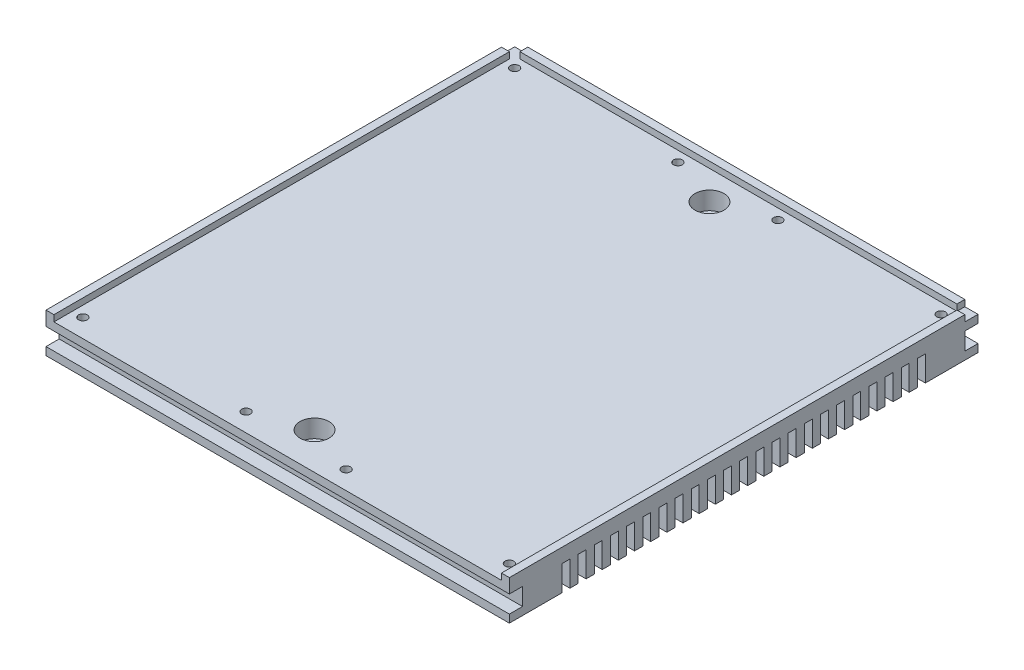
SolidWorks part; units mm, degrees
material "6061 合金"
ref_plane "前视基准面" through (0, 0, 0) normal (0, 0, 1) x (1, 0, 0)
ref_plane "上视基准面" through (0, 0, 0) normal (0, 1, 0) x (1, 0, 0)
ref_plane "右视基准面" through (0, 0, 0) normal (1, 0, 0) x (0, 0, -1)
sketch "草图1" plane through (0, 12.6, 0) normal (0, 1, 0) x (1, 0, 0)
  line L0 (-100.7481, -361.7245) -> (-100.7481, -517.7245) construction
  line L1 (72.2519, -528.7245) -> (-103.7481, -528.7245)
  line L2 (72.2519, -528.7245) -> (72.2519, -350.7245)
  line L3 (72.2519, -350.7245) -> (-103.7481, -350.7245)
  line L4 (-103.7481, -528.7245) -> (-103.7481, -350.7245)
  line L5 (7.2519, -525.7245) -> (61.2519, -525.7245) construction
  line L6 (69.2519, -517.7245) -> (69.2519, -361.7245) construction
  line L9 (61.2519, -353.7245) -> (7.2519, -353.7245) construction
  dimension "D1" = 3
  dimension "D2" = 3
  dimension "D3" = 3
  dimension "D4" = 3
extrude "凸台-拉伸1" add sketch "草图1" against normal up to surface (12.6 mm away)
sketch "草图3" plane through (0, 12.6, 0) normal (0, 1, 0) x (1, 0, 0)
  line L0 (-15.7481, -539.7245) -> (-15.7481, -489.7245) construction
  line L1 (-15.7481, -489.7245) -> (-15.7481, -389.7245) construction
  dimension "D1" = 50
  dimension "D2" = 100
hole_wizard "打孔尺寸(%根据)内六角圆柱头螺钉的类型1" [suppressed] positions "3D草图1" profile "草图4" counterbore size "M6" standard "GB"
sketch3d "3D草图1"
  point P0 (-15.7481, 12.6, 389.7245)
  point P3 (-15.7481, 12.6, 489.7245)
sketch "草图4" plane through (-15.7481, 12.6, 389.7245) normal (1, 0, 0) x (0, 0, 1)
  line L0 (0, 0) -> (0, 12.6)
  line L1 (0, 12.6) -> (3.3, 12.6)
  line L3 (3.3, 12.6) -> (3.3, 7)
  line L4 (3.3, 7) -> (5.5, 7)
  line L5 (5.5, 7) -> (5.5, 0)
  line L7 (5.5, 0) -> (0, 0)
  line L11 (0, -6.35) -> (0, 107.95) construction
  dimension "通孔孔直径" = 6.6
  dimension "通孔孔深度" = 12.6
  dimension "柱形沉头孔直径" = 11
  dimension "柱形沉头孔深度" = 7
sketch "草图5" plane through (0, 0, 528.7245) normal (0, 0, 1) x (1, 0, 0)
  line L0 (72.2519, 0) -> (-103.7481, 0) construction
  line L1 (-98.7481, 0) -> (-96.7481, 0)
  line L2 (-98.7481, 0) -> (-98.7481, 7.6)
  line L3 (-98.7481, 7.6) -> (-96.7481, 7.6)
  line L4 (-96.7481, 0) -> (-96.7481, 7.6)
  line L5 (-103.7481, 0) -> (-103.7481, 12.6) construction
  line L6 (-103.7481, 12.6) -> (72.2519, 12.6) construction
  dimension "D1" = 5
  dimension "D2" = 5
  dimension "D3" = 2
extrude "切除-拉伸2" [suppressed] cut sketch "草图5" against normal through all
pattern_linear "阵列(线性)1" [suppressed] count 30 spacing 5.6552
sketch "草图6" [suppressed] plane through (0, 0, 0) normal (0, -1, 0) x (1, 0, 0)
  line L0 (-8.2654, 528.7245) -> (-23.2309, 528.7245) construction
  line L1 (-19.5757, 528.7245) -> (-17.5757, 528.7245)
  line L2 (-19.5757, 528.7245) -> (-19.5757, 498.7245)
  line L3 (-19.5757, 498.7245) -> (-17.5757, 498.7245)
  line L4 (-17.5757, 528.7245) -> (-17.5757, 498.7245)
  line L5 (-25.2309, 528.7245) -> (-23.2309, 528.7245) construction
  line L6 (-25.2309, 528.7245) -> (-28.8861, 528.7245) construction
  line L7 (-19.5757, 528.7245) -> (-23.2309, 528.7245) construction
  line L8 (-17.5757, 528.7245) -> (-13.9205, 528.7245) construction
  line L9 (-13.9205, 528.7245) -> (-11.9205, 528.7245)
  line L10 (-13.9205, 528.7245) -> (-13.9205, 498.7245)
  line L11 (-13.9205, 498.7245) -> (-11.9205, 498.7245)
  line L12 (-11.9205, 528.7245) -> (-11.9205, 498.7245)
  line L13 (-23.2309, 350.7245) -> (-8.2654, 350.7245) construction
  line L14 (-19.5757, 350.7245) -> (-17.5757, 350.7245)
  line L15 (-19.5757, 350.7245) -> (-19.5757, 380.7245)
  line L16 (-19.5757, 380.7245) -> (-17.5757, 380.7245)
  line L17 (-17.5757, 350.7245) -> (-17.5757, 380.7245)
  line L19 (-13.9205, 350.7245) -> (-11.9205, 350.7245)
  line L20 (-13.9205, 350.7245) -> (-13.9205, 380.7245)
  line L21 (-13.9205, 380.7245) -> (-11.9205, 380.7245)
  line L22 (-11.9205, 350.7245) -> (-11.9205, 380.7245)
  dimension "D1" = 30
  dimension "D2" = 30
extrude "切除-拉伸3" [suppressed] cut sketch "草图6" against normal up to surface (7.6 mm away)
sketch "草图7" plane through (0, 12.6, 0) normal (0, 1, 0) x (1, 0, 0)
  line L0 (69.2519, -528.7245) -> (69.2519, -353.7245)
  line L1 (69.2519, -353.7245) -> (-100.7481, -353.7245)
  line L2 (-100.7481, -353.7245) -> (-100.7481, -528.7245)
  line L3 (69.2519, -528.7245) -> (72.2519, -528.7245)
  line L4 (72.2519, -528.7245) -> (72.2519, -350.7245)
  line L5 (72.2519, -350.7245) -> (-103.7481, -350.7245)
  line L6 (-103.7481, -350.7245) -> (-103.7481, -528.7245)
  line L7 (-103.7481, -528.7245) -> (72.2519, -528.7245)
  line L8 (72.2519, -528.7245) -> (72.2519, -350.7245)
  line L9 (72.2519, -350.7245) -> (-103.7481, -350.7245)
  line L10 (-103.7481, -350.7245) -> (-103.7481, -528.7245)
  line L11 (-103.7481, -528.7245) -> (-100.7481, -528.7245)
  dimension "D1" = 0
  dimension "D2" = 3
extrude "凸台-拉伸3" add sketch "草图7" along normal offset from surface (2.4 mm away) 15 up to face at (-15.7481, 0, 439.7245)
sketch "草图8" plane through (0, 15, 0) normal (0, 1, 0) x (1, 0, 0)
  line L1 (-103.7481, -350.7245) -> (-98.7481, -350.7245)
  line L2 (-103.7481, -350.7245) -> (-103.7481, -355.7245)
  line L3 (-103.7481, -355.7245) -> (-98.7481, -355.7245)
  line L4 (-98.7481, -350.7245) -> (-98.7481, -355.7245)
  line L5 (72.2519, -350.7245) -> (67.2519, -350.7245)
  line L6 (72.2519, -350.7245) -> (72.2519, -355.7245)
  line L7 (72.2519, -355.7245) -> (67.2519, -355.7245)
  line L8 (67.2519, -350.7245) -> (67.2519, -355.7245)
  dimension "D1" = 5
  dimension "D2" = 5
  dimension "D3" = 5
  dimension "D4" = 5
extrude "切除-拉伸4" cut sketch "草图8" against normal up to surface (2.4 mm away) up to face at (-15.7481, 12.6, 441.2245)
sketch "草图9" plane through (0, 12.6, 0) normal (0, 1, 0) x (1, 0, 0)
  line L1 (-96.7481, -357.7245) -> (-34.7481, -357.7245)
  line L2 (-96.7481, -357.7245) -> (-96.7481, -521.7245)
  line L3 (-96.7481, -521.7245) -> (-34.7481, -521.7245)
  line L4 (-34.7481, -357.7245) -> (-34.7481, -521.7245)
  line L5 (3.2519, -521.7245) -> (65.2519, -521.7245)
  line L6 (3.2519, -521.7245) -> (3.2519, -357.7245)
  line L7 (3.2519, -357.7245) -> (65.2519, -357.7245)
  line L8 (65.2519, -521.7245) -> (65.2519, -357.7245)
hole_wizard "M4 螺纹孔1" positions "3D草图2" profile "草图10" tap size "M4" standard "GB"
sketch3d "3D草图2"
  point P0 (-96.7481, 12.6, 357.7245)
  point P3 (-34.7481, 12.6, 357.7245)
  point P6 (-34.7481, 12.6, 521.7245)
  point P9 (-96.7481, 12.6, 521.7245)
  point P12 (3.2519, 12.6, 521.7245)
  point P15 (65.2519, 12.6, 521.7245)
  point P18 (65.2519, 12.6, 357.7245)
  point P21 (3.2519, 12.6, 357.7245)
sketch "草图10" plane through (-96.7481, 12.6, 357.7245) normal (1, 0, 0) x (0, 0, 1)
  line L0 (0, 0) -> (0, 5.9914)
  line L1 (0, 5.9914) -> (1.65, 5)
  line L2 (1.65, 5) -> (1.65, 0)
  line L5 (1.65, 0) -> (0, 0)
  line L10 (0, 5.9914) -> (-1.65, 5) construction
  line L11 (0, -6.35) -> (0, 107.95) construction
  dimension "螺纹孔钻头直径" = 3.3
  dimension "螺纹孔钻头深度" = 5
  dimension "导头角度" = 118
cosmetic thread "孔螺蚊线1" parameters "D1"=5, "D2"=4
cosmetic thread "孔螺蚊线2" parameters "D1"=5, "D2"=4
cosmetic thread "孔螺蚊线3" parameters "D1"=5, "D2"=4
cosmetic thread "孔螺蚊线4" parameters "D1"=5, "D2"=4
cosmetic thread "孔螺蚊线5" parameters "D1"=5, "D2"=4
cosmetic thread "孔螺蚊线6" parameters "D1"=5, "D2"=4
cosmetic thread "孔螺蚊线7" parameters "D1"=5, "D2"=4
cosmetic thread "孔螺蚊线8" parameters "D1"=5, "D2"=4
sketch "草图11" [suppressed] plane through (0, 0, 0) normal (0, -1, 0) x (1, 0, 0)
  line L0 (-15.7481, 489.7245) -> (-15.7481, 479.7245) construction
  line L1 (-15.7481, 489.7245) -> (-15.7481, 389.7245) construction
  line L2 (-15.7481, 389.7245) -> (-15.7481, 399.7245) construction
  dimension "D1" = 10
  dimension "D2" = 10
hole_wizard "大小mm 暗销孔1" [suppressed] positions "3D草图3" profile "草图12" hole size "Ø4.0" standard "GB"
sketch3d "3D草图3" [suppressed]
  point P0 (-15.7481, 0, 479.7245)
sketch "草图12" plane through (-15.7481, 0, 479.7245) normal (1, 0, 0) x (0, 0, -1)
  line L0 (0, 0) -> (0, 6.2017)
  line L1 (0, 6.2017) -> (2, 5)
  line L2 (2, 5) -> (2, 0)
  line L5 (2, 0) -> (0, 0)
  line L10 (0, 6.2017) -> (-2, 5) construction
  line L11 (0, -6.35) -> (0, 107.95) construction
  dimension "孔直径" = 4
  dimension "孔深度" = 5
  dimension "导头角度" = 118
sketch "草图13" [suppressed] plane through (0, 0, 0) normal (0, -1, 0) x (1, 0, 0)
  line L0 (-15.7481, 398.7245) -> (-15.7481, 400.7245) construction
  line L1 (-15.7481, 489.7245) -> (-15.7481, 389.7245) construction
  line L2 (-17.7481, 398.7245) -> (-17.7481, 400.7245)
  line L3 (-13.7481, 398.7245) -> (-13.7481, 400.7245)
  arc A0 (-17.7481, 398.7245) -> (-13.7481, 398.7245) centre (-15.7481, 398.7245) ccw
  arc A1 (-13.7481, 400.7245) -> (-17.7481, 400.7245) centre (-15.7481, 400.7245) ccw
  point P5 (-15.7481, 399.7245)
  dimension "D1" = 2
  dimension "D2" = 2
extrude "切除-拉伸5" [suppressed] cut sketch "草图13" against normal blind 5
sketch "草图14" plane through (-103.7481, 0, 0) normal (-1, 0, 0) x (0, 0, 1)
  line L0 (355.7245, 12.6) -> (350.7245, 12.6) construction
  line L1 (528.7245, 3) -> (523.7245, 3)
  line L2 (528.7245, 3) -> (528.7245, 9.6)
  line L3 (528.7245, 9.6) -> (523.7245, 9.6)
  line L4 (523.7245, 3) -> (523.7245, 9.6)
  line L5 (350.7245, 3) -> (355.7245, 3)
  line L6 (350.7245, 3) -> (350.7245, 9.6)
  line L7 (350.7245, 9.6) -> (355.7245, 9.6)
  line L8 (355.7245, 3) -> (355.7245, 9.6)
  line L9 (528.7245, 0) -> (350.7245, 0) construction
  line L10 (528.7245, 0) -> (528.7245, 15) construction
  dimension "D1" = 3
  dimension "D2" = 3
  dimension "D3" = 5
extrude "切除-拉伸6" cut sketch "草图14" against normal through all
sketch "草图15" plane through (-103.7481, 0, 0) normal (-1, 0, 0) x (0, 0, 1)
  line L0 (528.7245, 0) -> (350.7245, 0) construction
  line L1 (508.7245, 0) -> (505.7245, 0)
  line L2 (508.7245, 0) -> (508.7245, 9.6)
  line L3 (508.7245, 9.6) -> (505.7245, 9.6)
  line L4 (505.7245, 0) -> (505.7245, 9.6)
  line L5 (523.7245, 9.6) -> (523.7245, 3) construction
  line L6 (528.7245, 9.6) -> (523.7245, 9.6) construction
  dimension "D1" = 3
  dimension "D2" = 15
extrude "切除-拉伸7" cut sketch "草图15" against normal through all
pattern_linear "阵列(线性)3" count 23 spacing 6.1364 along (0, 0, -1) of "切除-拉伸7"
sketch "草图16" plane through (0, 0, 0) normal (0, -1, 0) x (1, 0, 0)
  line L0 (-103.7481, 481.1791) -> (-103.7481, 478.0427) construction
  line L1 (-103.7481, 478.0427) -> (-23.2481, 478.0427)
  line L2 (-103.7481, 478.0427) -> (-103.7481, 475.0427)
  line L3 (-103.7481, 475.0427) -> (-23.2481, 475.0427)
  line L4 (-23.2481, 478.0427) -> (-23.2481, 475.0427)
  line L5 (72.2519, 453.4972) -> (72.2519, 456.6336) construction
  line L6 (72.2519, 478.0427) -> (-8.2481, 478.0427)
  line L7 (72.2519, 478.0427) -> (72.2519, 475.0427)
  line L8 (72.2519, 475.0427) -> (-8.2481, 475.0427)
  line L9 (-8.2481, 478.0427) -> (-8.2481, 475.0427)
  line L10 (-15.7481, 539.7245) -> (-15.7481, 489.7245) construction
  line L11 (-15.7481, 489.7245) -> (-15.7481, 389.7245) construction
  line L12 (-103.7481, 484.1791) -> (-103.7481, 481.1791) construction
  line L13 (-103.7481, 478.0427) -> (-103.7481, 481.1791) construction
  line L14 (-103.7481, 487.3154) -> (-103.7481, 484.1791) construction
  dimension "D1" = 7.5
  dimension "D2" = 7.5
extrude "切除-拉伸8" [suppressed] cut sketch "草图16" against normal up to surface (9.6 mm away)
pattern_linear "阵列(线性)4" [suppressed] count 27 spacing 5.0323
sketch "草图17" plane through (0, 12.6, 0) normal (0, 1, 0) x (1, 0, 0)
  line L0 (-15.7481, -389.7245) -> (-15.7481, -364.7245) construction
  line L1 (67.2519, -350.7245) -> (-98.7481, -350.7245) construction
  line L2 (-15.7481, -528.7245) -> (-15.7481, -514.7245) construction
  line L3 (-100.7481, -528.7245) -> (69.2519, -528.7245) construction
  line L4 (-15.7481, -539.7245) -> (-15.7481, -489.7245) construction
  dimension "D1" = 14
  dimension "D2" = 14
hole_wizard "打孔尺寸(%根据)内六角圆柱头螺钉的类型2" positions "3D草图5" profile "草图19" counterbore size "M6" standard "GB" end condition through all
sketch3d "3D草图5"
  point P0 (-15.7481, 12.6, 514.7245)
  point P3 (-15.7481, 12.6, 364.7245)
sketch "草图19" plane through (-15.7481, 12.6, 514.7245) normal (1, 0, 0) x (0, 0, 1)
  line L0 (0, 0) -> (0, 12.6)
  line L1 (0, 12.6) -> (3.3, 12.6)
  line L3 (3.3, 12.6) -> (3.3, 6.8)
  line L4 (3.3, 6.8) -> (5.5, 6.8)
  line L5 (5.5, 6.8) -> (5.5, 0)
  line L7 (5.5, 0) -> (0, 0)
  line L11 (0, -6.35) -> (0, 107.95) construction
  dimension "通孔孔直径" = 6.6
  dimension "通孔孔深度" = 12.6
  dimension "柱形沉头孔直径" = 11
  dimension "柱形沉头孔深度" = 6.8
sketch "草图20" plane through (0, 0, 0) normal (0, -1, 0) x (1, 0, 0)
  line L0 (-15.7481, 514.7245) -> (-5.7481, 514.7245) construction
  line L1 (-15.7481, 364.7245) -> (-5.7481, 364.7245) construction
  dimension "D1" = 10
hole_wizard "大小mm 暗销孔2" positions "3D草图6" profile "草图21" hole size "Ø4.0" standard "GB"
sketch3d "3D草图6"
  point P3 (-5.7481, 0, 364.7245)
sketch "草图21" plane through (-5.7481, 0, 364.7245) normal (1, 0, 0) x (0, 0, -1)
  line L0 (0, 0) -> (0, 6.2017)
  line L1 (0, 6.2017) -> (2, 5)
  line L2 (2, 5) -> (2, 0)
  line L5 (2, 0) -> (0, 0)
  line L10 (0, 6.2017) -> (-2, 5) construction
  line L11 (0, -6.35) -> (0, 107.95) construction
  dimension "孔直径" = 4
  dimension "孔深度" = 5
  dimension "导头角度" = 118
sketch "草图22" plane through (0, 0, 0) normal (0, -1, 0) x (1, 0, 0)
  line L0 (-5.7481, 513.7245) -> (-5.7481, 515.7245) construction
  line L1 (-7.7481, 513.7245) -> (-7.7481, 515.7245)
  line L2 (-3.7481, 513.7245) -> (-3.7481, 515.7245)
  arc A0 (-7.7481, 513.7245) -> (-3.7481, 513.7245) centre (-5.7481, 513.7245) ccw
  arc A1 (-3.7481, 515.7245) -> (-7.7481, 515.7245) centre (-5.7481, 515.7245) ccw
  point P2 (-5.7481, 514.7245)
  dimension "D1" = 2
  dimension "D2" = 2
extrude "切除-拉伸11" cut sketch "草图22" against normal blind 5
